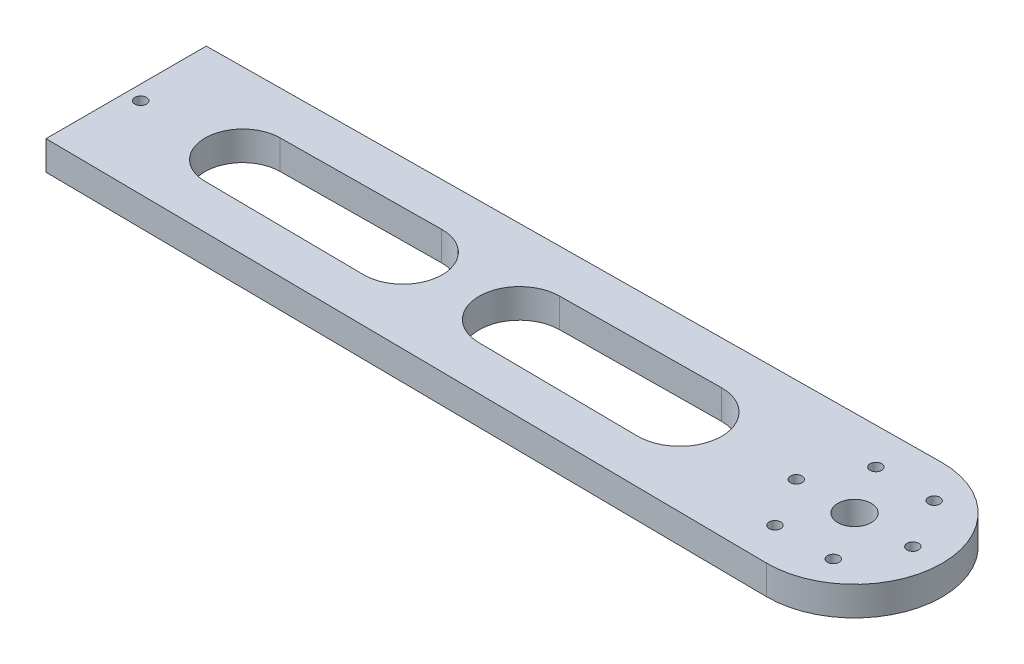
SolidWorks part; units mm, degrees
material "Acrylic (Medium-high impact)"
ref_plane "Front Plane" through (0, 0, 0) normal (0, 0, 1) x (1, 0, 0)
ref_plane "Top Plane" through (0, 0, 0) normal (0, 1, 0) x (1, 0, 0)
ref_plane "Right Plane" through (0, 0, 0) normal (1, 0, 0) x (0, 0, -1)
sketch "Sketch1" plane through (0, 0, 0) normal (0, 1, 0) x (1, 0, 0)
  line L0 (-216.3821, 37.4794) -> (33.318, 39.9538)
  line L1 (-216.3874, -17.5206) -> (33.3122, -20.0432)
  line L2 (-176.5126, 22.8737) -> (-121.518, 23.4187)
  line L3 (-216.3821, 37.4794) -> (-216.3874, -17.5206)
  line L4 (-196.1968, 9.9774) -> (296.6541, 9.9298) construction
  line L5 (-176.5151, -2.9227) -> (-121.5206, -3.4783)
  line L6 (-81.5247, -3.8823) -> (-26.5302, -4.4379)
  line L7 (-81.522, 23.815) -> (-26.5274, 24.36)
  circle A0 centre (33.6152, 9.9552) radius 5.75
  arc A1 (33.3122, -20.0432) -> (33.318, 39.9538) centre (33.6152, 9.9552) ccw
  circle A2 centre (33.6152, 9.9552) radius 20 construction
  circle A3 centre (53.6152, 9.9552) radius 2
  circle A4 centre (43.6152, -7.3653) radius 2
  circle A5 centre (23.6152, -7.3653) radius 2
  circle A6 centre (13.6152, 9.9552) radius 2
  circle A7 centre (23.6152, 27.2757) radius 2
  circle A8 centre (43.6152, 27.2757) radius 2
  arc A9 (-176.5126, 22.8737) -> (-176.5151, -2.9227) centre (-176.3848, 9.9755) ccw
  arc A10 (-26.5302, -4.4379) -> (-26.5274, 24.36) centre (-26.3848, 9.961) ccw
  arc A11 (-121.5206, -3.4783) -> (-121.518, 23.4187) centre (-121.3848, 9.9702) ccw
  arc A12 (-81.522, 23.815) -> (-81.5247, -3.8823) centre (-81.3848, 9.9663) ccw
  circle A13 centre (-211.3848, 9.9794) radius 2
  point P36 (33.6152, 9.9552)
  dimension "D1" = 60
  dimension "D2" = 11.5
  dimension "D3" = 40
  dimension "D4" = 4
  dimension "D6" = 55
  dimension "D7" = 27.5
  dimension "D8" = 15
  dimension "D14" = 27.5
  dimension "D15" = 5
  dimension "D13" = 4
  dimension "D9" = 40
  dimension "D10" = 55
  dimension "D11" = 60
  dimension "D12" = 55
  dimension "D22" = 250
  dimension "D5" = 6
extrude "Boss-Extrude1" add sketch "Sketch1" along normal blind 10
